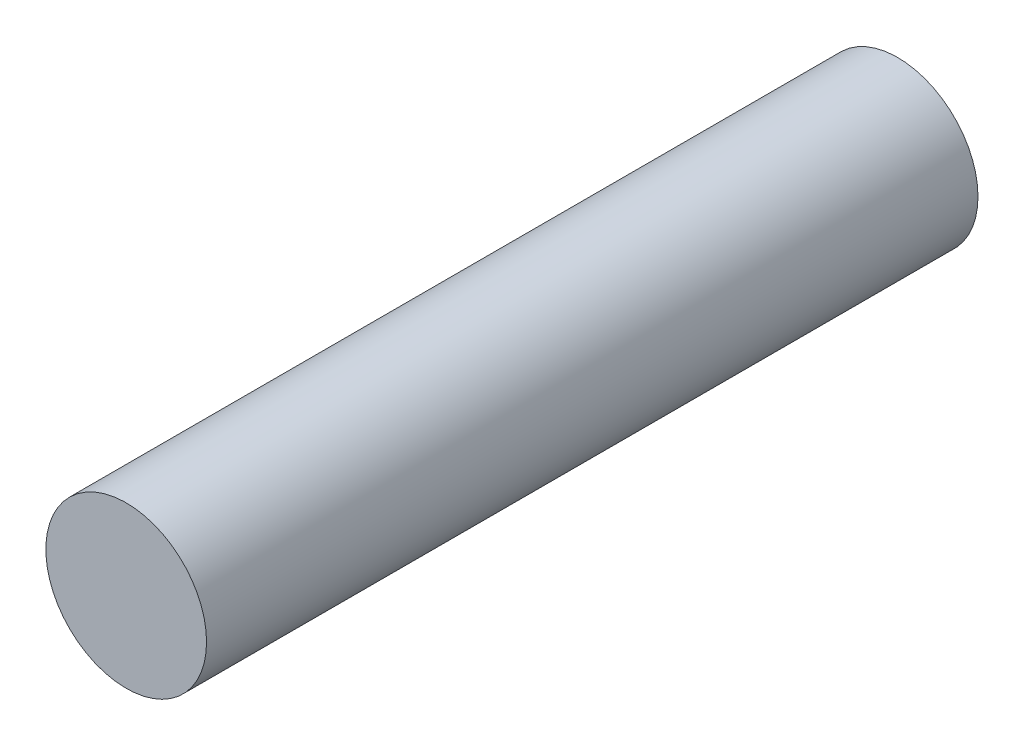
SolidWorks part; units mm, degrees
material "1060 合金"
ref_plane "前视基准面" through (0, 0, 0) normal (0, 0, 1) x (1, 0, 0)
ref_plane "上视基准面" through (0, 0, 0) normal (0, 1, 0) x (1, 0, 0)
ref_plane "右视基准面" through (0, 0, 0) normal (1, 0, 0) x (0, 0, -1)
sketch "草图1" plane through (0, 0, 0) normal (0, 0, 1) x (1, 0, 0)
  circle A0 centre (0, 0) radius 2.5
  dimension "D1" = 5
extrude "凸台-拉伸1" add sketch "草图1" along normal blind 24
